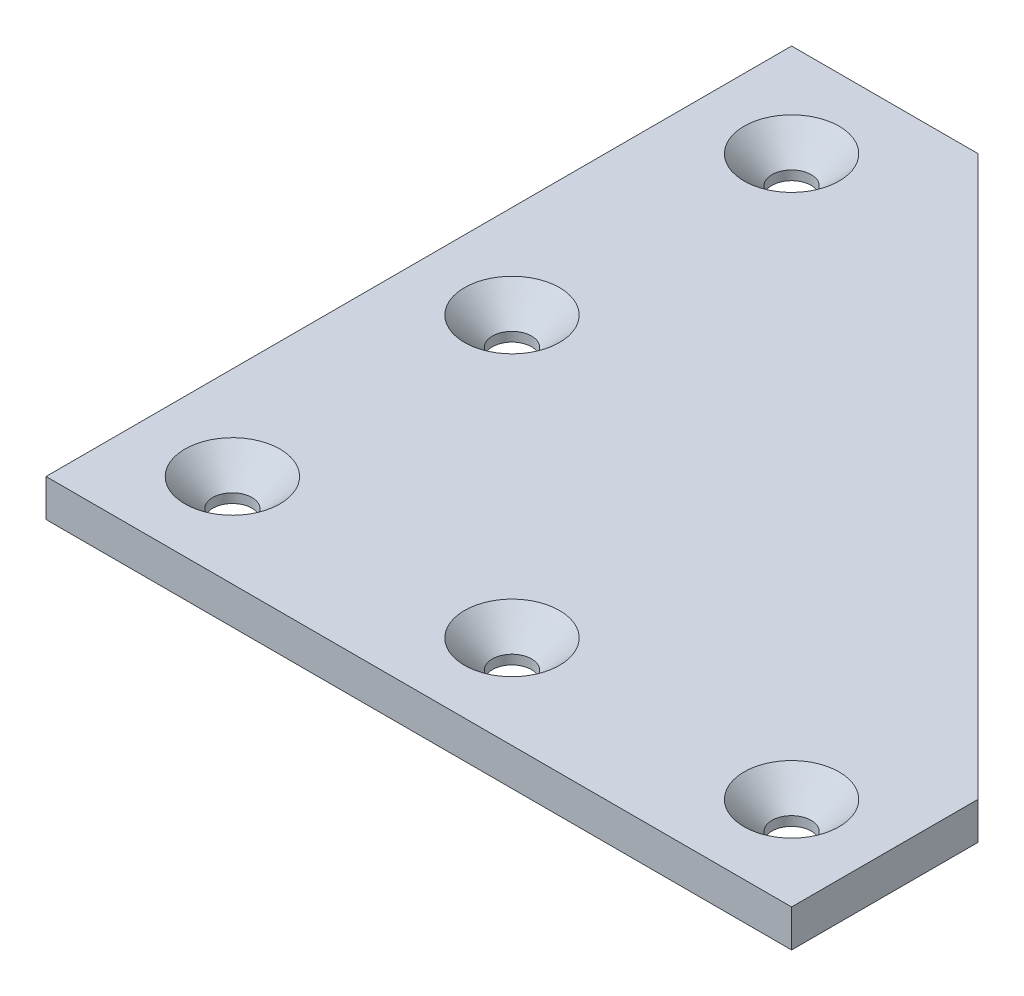
SolidWorks part; units mm, degrees
material "1060 Alloy"
ref_plane "Front Plane" through (0, 0, 0) normal (0, 0, 1) x (1, 0, 0)
ref_plane "Top Plane" through (0, 0, 0) normal (0, 1, 0) x (1, 0, 0)
ref_plane "Right Plane" through (0, 0, 0) normal (1, 0, 0) x (0, 0, -1)
sketch "Sketch1" plane through (0, 0, 0) normal (0, 1, 0) x (1, 0, 0)
  line L0 (0, 0) -> (0, 80)
  line L1 (0, 80) -> (20, 80)
  line L2 (20, 80) -> (80, 20)
  line L3 (80, 20) -> (80, 0)
  line L4 (80, 0) -> (0, 0)
  dimension "D1" = 20
  dimension "D2" = 20
  dimension "D3" = 45
  dimension "D4" = 80
extrude "Boss-Extrude1" add sketch "Sketch1" along normal blind 4
fillet "Fillet1" [suppressed] radius 1
sketch "Sketch3" plane through (0, 4, 0) normal (0, 1, 0) x (1, 0, 0)
  line L0 (0, 80) -> (0, 0) construction
  line L1 (0, 0) -> (80, 0) construction
  line L3 (80, 0) -> (80, 20) construction
  line L4 (20, 80) -> (0, 80) construction
  circle A2 centre (10, 10) radius 2.1
  circle A5 centre (40, 10) radius 2.1
  circle A6 centre (70, 10) radius 2.1
  circle A7 centre (10, 40) radius 2.1
  circle A8 centre (10, 70) radius 2.1
  dimension "D3" = 4.2
  dimension "D7" = 10
  dimension "D1" = 10
  dimension "D2" = 10
  dimension "D4" = 3
  dimension "D6" = 10
  dimension "D5" = 3
extrude "Cut-Extrude1" cut sketch "Sketch3" against normal blind 4
chamfer "Chamfer1" distance 3 angle 45 5 edges at (70, 4, -7.9) (40, 4, -7.9) (10, 4, -7.9) (10, 4, -37.9) (10, 4, -67.9)
